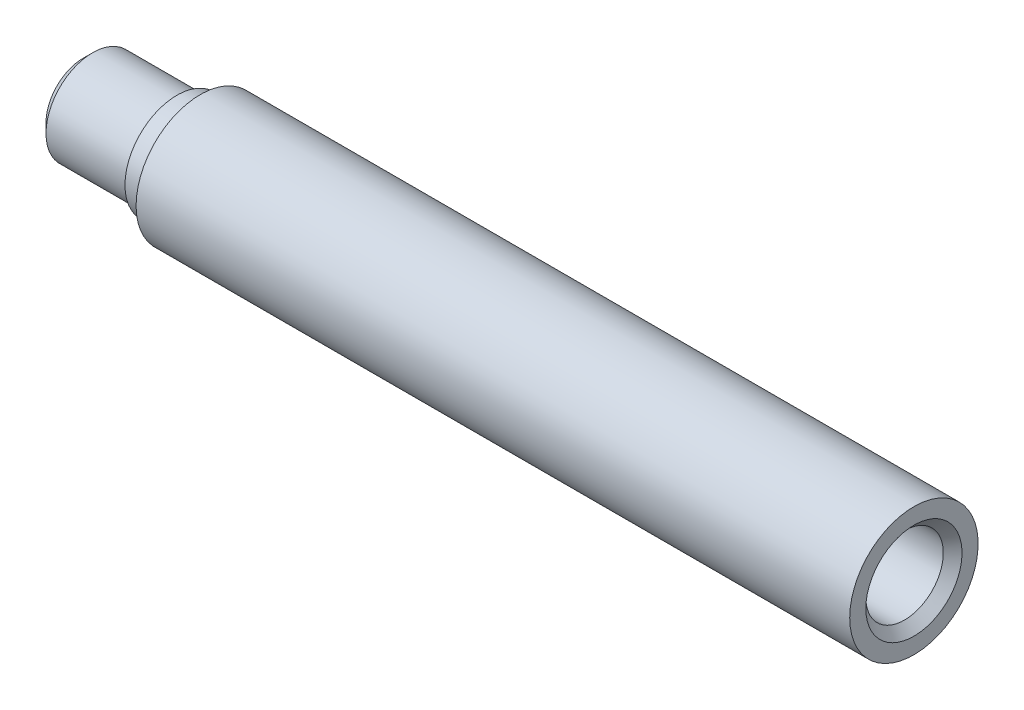
SolidWorks part; units mm, degrees
ref_plane "Front Plane" through (0, 0, 0) normal (0, 0, 1) x (1, 0, 0)
ref_plane "Top Plane" through (0, 0, 0) normal (0, 1, 0) x (1, 0, 0)
ref_plane "Right Plane" through (0, 0, 0) normal (1, 0, 0) x (0, 0, -1)
ref_plane "Plane1" through (0, 0, 0) normal (0, 0, -1) x (-1, 0, 0)
sketch "Sketch1" plane through (0, 0, 0) normal (0, 0, -1) x (-1, 0, 0)
  line L0 (-19, 3.3114) -> (-17.0103, 0)
  line L1 (-17.0103, 0) -> (36, 0)
  line L2 (36, 0) -> (36, 3.1879)
  line L3 (36, 3.1879) -> (35.2, 3.9879)
  line L4 (35.2, 3.9879) -> (28, 3.9879)
  line L5 (28, 3.9879) -> (28, 4.4379)
  line L6 (28, 4.4379) -> (26, 4.4379)
  line L7 (26, 4.4379) -> (26, 5.4879)
  line L8 (26, 5.4879) -> (-35, 5.4879)
  line L9 (-35, 5.4879) -> (-35, 4.1114)
  line L10 (-35, 4.1114) -> (-34.2, 3.3114)
  line L11 (-34.2, 3.3114) -> (-19, 3.3114)
  line L12 (-35, 0) -> (36, 0) construction
revolve "Revolve1" add sketch "Sketch1" angle 360 about L12
